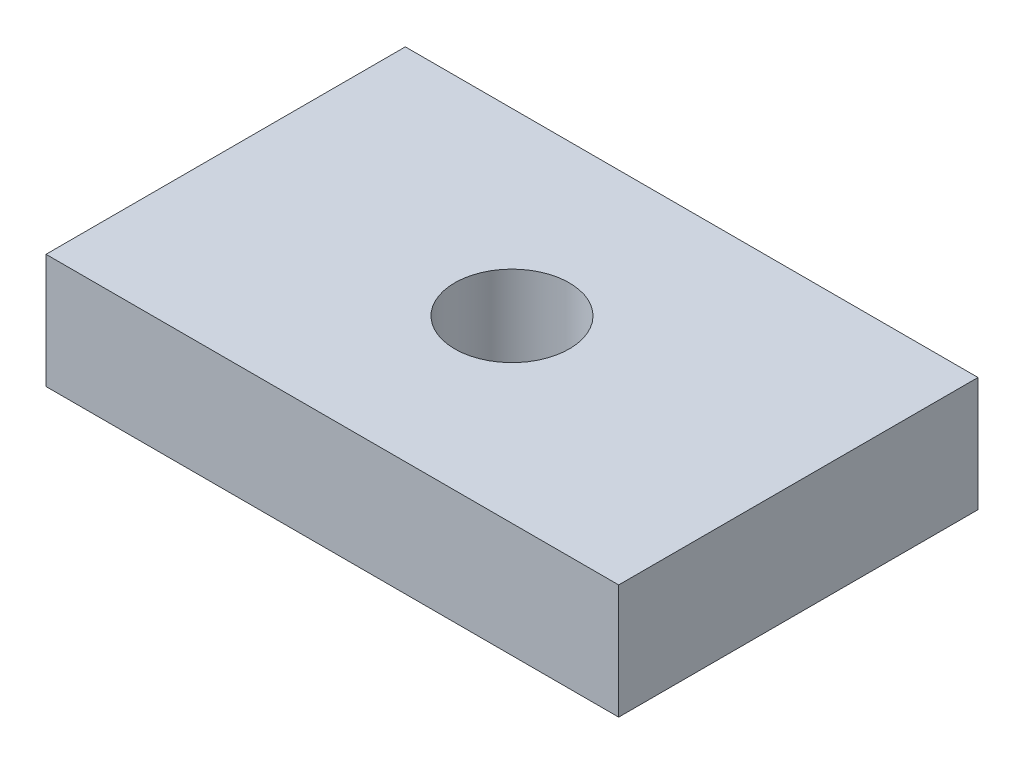
SolidWorks part; units mm, degrees
ref_plane "Front Plane" through (0, 0, 0) normal (0, 0, 1) x (1, 0, 0)
ref_plane "Top Plane" through (0, 0, 0) normal (0, 1, 0) x (1, 0, 0)
ref_plane "Right Plane" through (0, 0, 0) normal (1, 0, 0) x (0, 0, -1)
sketch "Sketch1" plane through (0, 0, 0) normal (0, 1, 0) x (1, 0, 0)
  line L0 (0, 0) -> (50, 31.372) construction
  line L1 (0, 0) -> (50, 0)
  line L2 (0, 0) -> (0, 31.372)
  line L3 (0, 31.372) -> (50, 31.372)
  line L4 (50, 0) -> (50, 31.372)
  circle A0 centre (25, 15.686) radius 5.0025
  dimension "D2" = 10.005
  dimension "D1" = 50
extrude "Boss-Extrude1" add sketch "Sketch1" along normal blind 10
